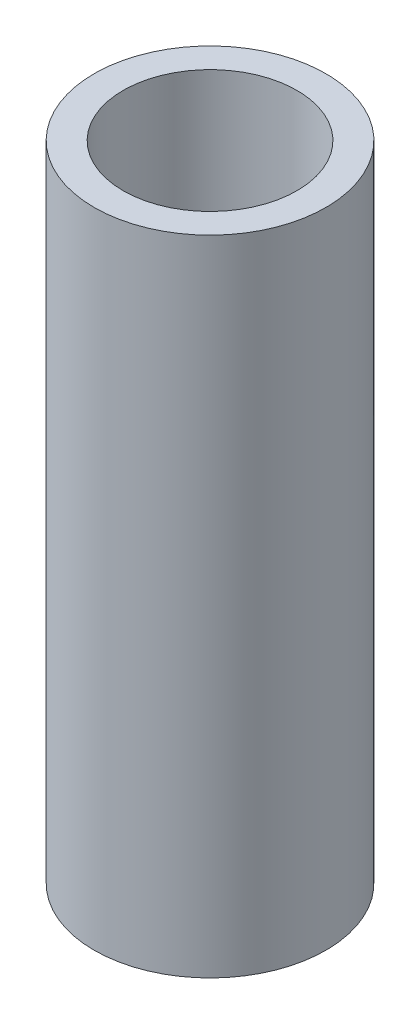
SolidWorks part; units mm, degrees
material "6061-T6 (SS)"
ref_plane "Front Plane" through (0, 0, 0) normal (0, 0, 1) x (1, 0, 0)
ref_plane "Top Plane" through (0, 0, 0) normal (0, 1, 0) x (1, 0, 0)
ref_plane "Right Plane" through (0, 0, 0) normal (1, 0, 0) x (0, 0, -1)
sketch "Sketch1" plane through (0, 0, 0) normal (0, 1, 0) x (1, 0, 0)
  circle A0 centre (0, 0) radius 19.05
  circle A1 centre (0, 0) radius 25.4
  dimension "D1" = 50.8
  dimension "D2" = 38.1
extrude "Boss-Extrude1" add sketch "Sketch1" along normal blind 141
